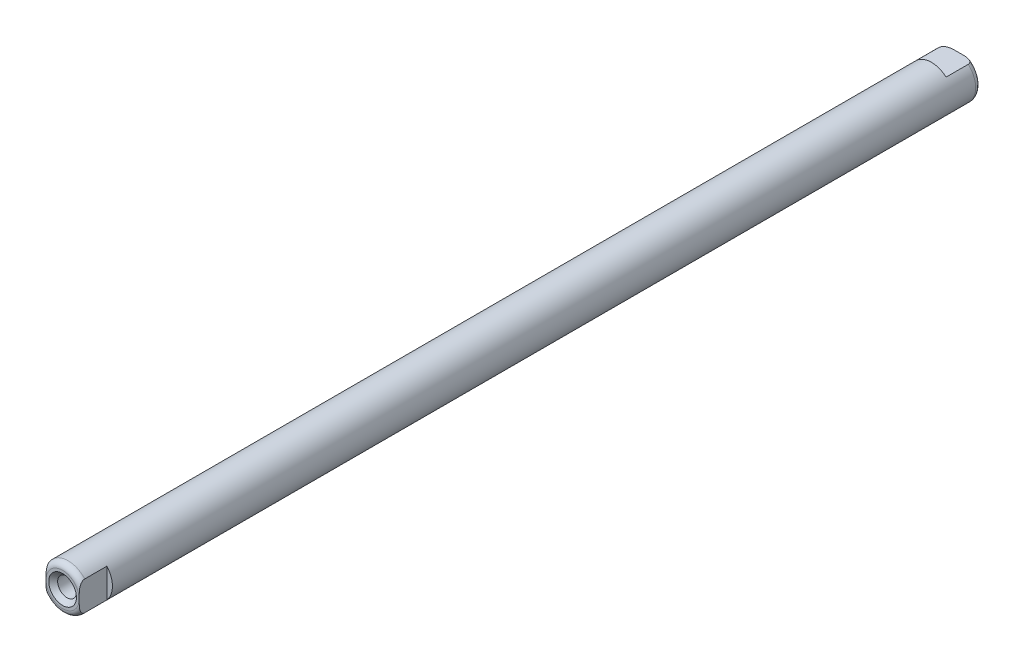
SolidWorks part; units mm, degrees
material "XC38"
ref_plane "Face" through (0, 0, 0) normal (0, 0, 1) x (1, 0, 0)
ref_plane "Dessus" through (0, 0, 0) normal (0, 1, 0) x (1, 0, 0)
ref_plane "Droite" through (0, 0, 0) normal (1, 0, 0) x (0, 0, -1)
sketch "Esquisse1" plane through (0, 0, 0) normal (0, 0, 1) x (1, 0, 0)
  circle A0 centre (0, 0) radius 8
  dimension "D1" = 16
extrude "Boss.-Extru.1" add sketch "Esquisse1" along normal mid plane 324
fillet "Congé1" radius 2 2 edges at (8, 0, -162) (8, 0, 162)
hole_wizard "Trou taraudé M81" positions "Esquisse3" profile "Esquisse2" tap size "M8" standard "ISO"
sketch "Esquisse3" plane through (0, 0, -162) normal (0, 0, -1) x (-1, 0, 0)
  point P0 (0, 0)
sketch "Esquisse2" plane through (0, 0, -162) normal (1, 0, 0) x (0, 1, 0)
  line L0 (0, 0) -> (0, 24.2929)
  line L1 (0, 24.2929) -> (3.4, 22.25)
  line L2 (3.4, 22.25) -> (3.4, 1.6)
  line L3 (3.4, 1.6) -> (5, 0)
  line L5 (5, 0) -> (0, 0)
  line L6 (-3.4, 1.6) -> (-5, 0) construction
  line L10 (0, 24.2929) -> (-3.4, 22.25) construction
  line L11 (0, -6.35) -> (0, 107.95) construction
  dimension "Diamètre du trou pour taraudage" = 6.8
  dimension "Profondeur du trou pour taraudage" = 22.25
  dimension "Diamètre du fraisage entrant" = 10
  dimension "Angle du fraisage entrant" = 90
  dimension "Angle de pointe" = 118
cosmetic thread "Filetage de perçage2" parameters "D1"=16, "D2"=8
mirror "Symétrie5" about plane through (0, 0, 0) normal (0, 0, 1) of "Trou taraudé M81"
sketch "Esquisse4" plane through (0, 0, -162) normal (0, 0, -1) x (-1, 0, 0)
  line L0 (0, 6) -> (0, -6) construction
  line L1 (-8, 6) -> (8, 6)
  line L2 (-8, 6) -> (-8, -6)
  line L3 (-8, -6) -> (8, -6)
  line L4 (8, 6) -> (8, -6)
  circle A0 centre (0, 0) radius 8 construction
  dimension "D1" = 12
extrude "Enlèv. mat.-Extru.1" cut sketch "Esquisse4" against normal blind 10 flip side to cut
sketch "Esquisse5" plane through (0, 0, 162) normal (0, 0, 1) x (1, 0, 0)
  line L0 (-6, 0) -> (6, 0) construction
  line L1 (-6, 8) -> (6, 8)
  line L2 (-6, 8) -> (-6, -8)
  line L3 (-6, -8) -> (6, -8)
  line L4 (6, 8) -> (6, -8)
  circle A0 centre (0, 0) radius 8 construction
  dimension "D1" = 12
extrude "Enlèv. mat.-Extru.2" cut sketch "Esquisse5" against normal blind 10 flip side to cut
